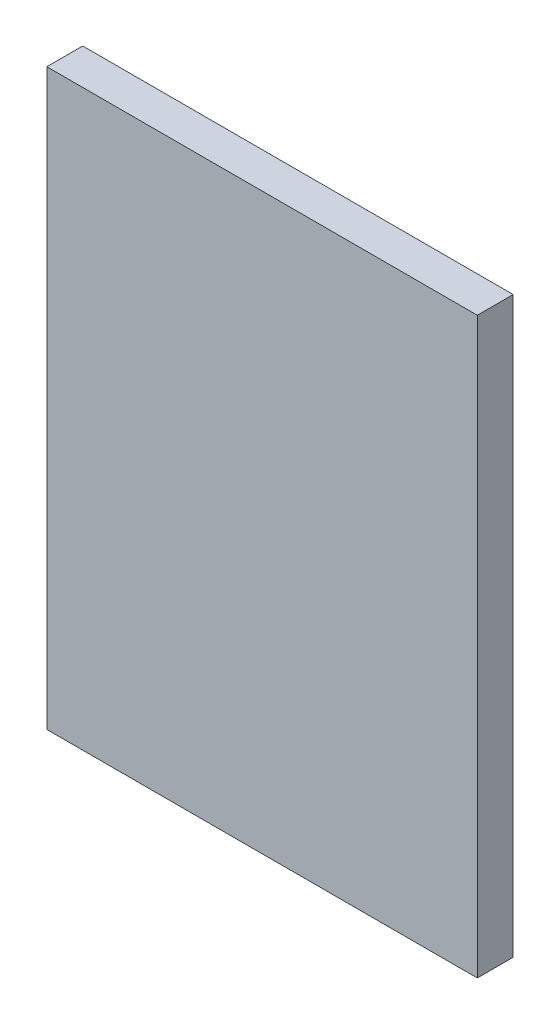
SolidWorks part; units mm, degrees
ref_plane "Front Plane" through (0, 0, 0) normal (0, 0, 1) x (1, 0, 0)
ref_plane "Top Plane" through (0, 0, 0) normal (0, 1, 0) x (1, 0, 0)
ref_plane "Right Plane" through (0, 0, 0) normal (1, 0, 0) x (0, 0, -1)
sketch "Sketch2" plane through (0, 0, 0) normal (0, 0, 1) x (1, 0, 0)
  line L1 (-19.05, -25.4) -> (19.05, -25.4)
  line L2 (-19.05, -25.4) -> (-19.05, 25.4)
  line L3 (-19.05, 25.4) -> (19.05, 25.4)
  line L4 (19.05, -25.4) -> (19.05, 25.4)
  line L5 (-19.05, -25.4) -> (19.05, 25.4) construction
  line L6 (-19.05, 25.4) -> (19.05, -25.4) construction
  point P0 (0, 0)
  dimension "D1" = 50.8
  dimension "D2" = 38.1
extrude "Boss-Extrude1" add sketch "Sketch2" along normal blind 3.175
